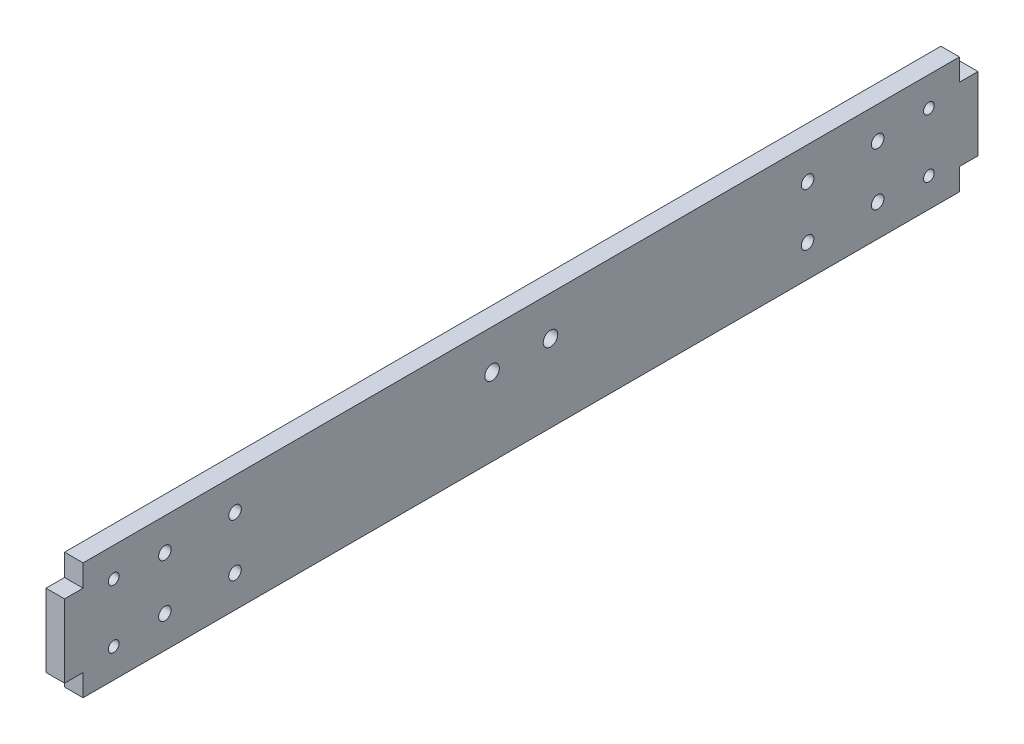
SolidWorks part; units mm, degrees
ref_plane "Front Plane" through (0, 0, 0) normal (0, 0, 1) x (1, 0, 0)
ref_plane "Top Plane" through (0, 0, 0) normal (0, 1, 0) x (1, 0, 0)
ref_plane "Right Plane" through (0, 0, 0) normal (1, 0, 0) x (0, 0, -1)
sketch "Sketch1" plane through (0, 0, 0) normal (1, 0, 0) x (0, 0, -1)
  line L0 (-150, -20) -> (-150, 20)
  line L1 (-150, -20) -> (150, -20)
  line L2 (-150, 20) -> (150, 20)
  line L3 (150, -20) -> (150, 20)
  line L4 (-150, -20) -> (150, 20) construction
  line L5 (-150, 20) -> (150, -20) construction
  point P1 (0, 0)
  dimension "D1" = 300
  dimension "D2" = 40
extrude "Boss-Extrude1" add sketch "Sketch1" along normal blind 6.35
sketch "Sketch2" plane through (6.35, 0, 0) normal (1, 0, 0) x (0, 0, -1)
  line L0 (-156.35, 12.5) -> (-150, 12.5)
  line L1 (-156.35, 12.5) -> (-156.35, -12.5)
  line L2 (-150, 12.5) -> (-150, -12.5)
  line L3 (-156.35, -12.5) -> (-150, -12.5)
  line L4 (-156.35, 12.5) -> (-150, -12.5) construction
  line L5 (-150, 12.5) -> (-156.35, -12.5) construction
  line L6 (156.35, 12.5) -> (150, 12.5)
  line L7 (156.35, 12.5) -> (156.35, -12.5)
  line L8 (150, 12.5) -> (150, -12.5)
  line L9 (156.35, -12.5) -> (150, -12.5)
  line L10 (156.35, 12.5) -> (150, -12.5) construction
  line L11 (150, 12.5) -> (156.35, -12.5) construction
  line L12 (-150, 20) -> (-150, -20) construction
  line L13 (150, -20) -> (150, 20) construction
  point P1 (-153.175, 0)
  point P2 (153.175, 0)
  dimension "D1" = 25
  dimension "D2" = 6.35
extrude "Boss-Extrude2" add sketch "Sketch2" against normal blind 6.35
sketch "Sketch3" plane through (6.35, 0, 0) normal (1, 0, 0) x (0, 0, -1)
  line L0 (10, 6.5) -> (-10, 6.5) construction
  point P3 (0, 6.5)
  dimension "D1" = 20
  dimension "D2" = 6.5
hole_wizard "#10 Clearance Hole1" positions "Sketch5" profile "Sketch4" hole size "#10" standard "ANSI Inch" end condition through all
sketch "Sketch5" plane through (6.35, 0, 0) normal (1, 0, 0) x (0, 0, -1)
  point P0 (-10, 6.5)
  point P3 (10, 6.5)
sketch "Sketch4" plane through (6.35, 6.5, 10) normal (0, 1, 0) x (0, 0, -1)
  line L0 (0, 0) -> (0, 6.35)
  line L1 (0, 6.35) -> (2.4892, 6.35)
  line L2 (2.4892, 6.35) -> (2.4892, 0)
  line L5 (2.4892, 0) -> (0, 0)
  line L11 (0, -6.35) -> (0, 107.95) construction
  dimension "Thru Hole Dia." = 4.9784
  dimension "Thru Hole Depth" = 6.35
sketch "Sketch6" plane through (6.35, 0, 0) normal (1, 0, 0) x (0, 0, -1)
  line L0 (-122, -9) -> (-98, -9) construction
  line L1 (-122, -9) -> (-122, 9) construction
  line L2 (-98, -9) -> (-98, 9) construction
  line L3 (-122, 9) -> (-98, 9) construction
  line L4 (-122, -9) -> (-98, 9) construction
  line L5 (-98, -9) -> (-122, 9) construction
  line L6 (122, -9) -> (122, 9) construction
  line L7 (122, -9) -> (98, -9) construction
  line L8 (122, 9) -> (98, 9) construction
  line L9 (98, -9) -> (98, 9) construction
  line L10 (122, -9) -> (98, 9) construction
  line L11 (122, 9) -> (98, -9) construction
  line L12 (-110, 0) -> (110, 0) construction
  point P1 (-110, 0)
  point P2 (110, 0)
  dimension "D1" = 24
  dimension "D2" = 18
  dimension "D3" = 220
hole_wizard "#8 Clearance Hole1" positions "Sketch8" profile "Sketch7" hole size "#8" standard "ANSI Inch" end condition through all
sketch "Sketch8" plane through (6.35, 0, 0) normal (1, 0, 0) x (0, 0, -1)
  point P0 (-122, 9)
  point P3 (-98, 9)
  point P6 (-98, -9)
  point P9 (-122, -9)
  point P12 (98, 9)
  point P15 (122, 9)
  point P18 (122, -9)
  point P21 (98, -9)
sketch "Sketch7" plane through (6.35, 9, 122) normal (0, 1, 0) x (0, 0, -1)
  line L0 (0, 0) -> (0, 6.35)
  line L1 (0, 6.35) -> (2.1526, 6.35)
  line L2 (2.1526, 6.35) -> (2.1526, 0)
  line L5 (2.1526, 0) -> (0, 0)
  line L11 (0, -6.35) -> (0, 107.95) construction
  dimension "Thru Hole Dia." = 4.3053
  dimension "Thru Hole Depth" = 6.35
sketch "Sketch9" plane through (6.35, 0, 0) normal (1, 0, 0) x (0, 0, -1)
  line L1 (-139.5352, 10) -> (-139.5352, -10) construction
  line L2 (139.5352, 10) -> (139.5352, -10) construction
  line L3 (-150, 20) -> (-150, 12.5) construction
  line L4 (150, 12.5) -> (150, 20) construction
  point P5 (-139.5352, 0)
  point P7 (139.5352, 0)
  dimension "D1" = 20
  dimension "D2" = 10.4648
  dimension "D3" = 10.4648
hole_wizard "#6 Clearance Hole1" positions "3DSketch1" profile "Sketch10" hole size "#6" standard "ANSI Inch" end condition through all
sketch3d "3DSketch1"
  point P0 (6.35, 10, 139.5352)
  point P3 (6.35, -10, 139.5352)
  point P6 (6.35, 10, -139.5352)
  point P9 (6.35, -10, -139.5352)
sketch "Sketch10" plane through (6.35, 10, 139.5352) normal (0, 1, 0) x (0, 0, -1)
  line L0 (0, 0) -> (0, 6.35)
  line L1 (0, 6.35) -> (1.8288, 6.35)
  line L2 (1.8288, 6.35) -> (1.8288, 0)
  line L5 (1.8288, 0) -> (0, 0)
  line L11 (0, -6.35) -> (0, 107.95) construction
  dimension "Thru Hole Dia." = 3.6576
  dimension "Thru Hole Depth" = 6.35
